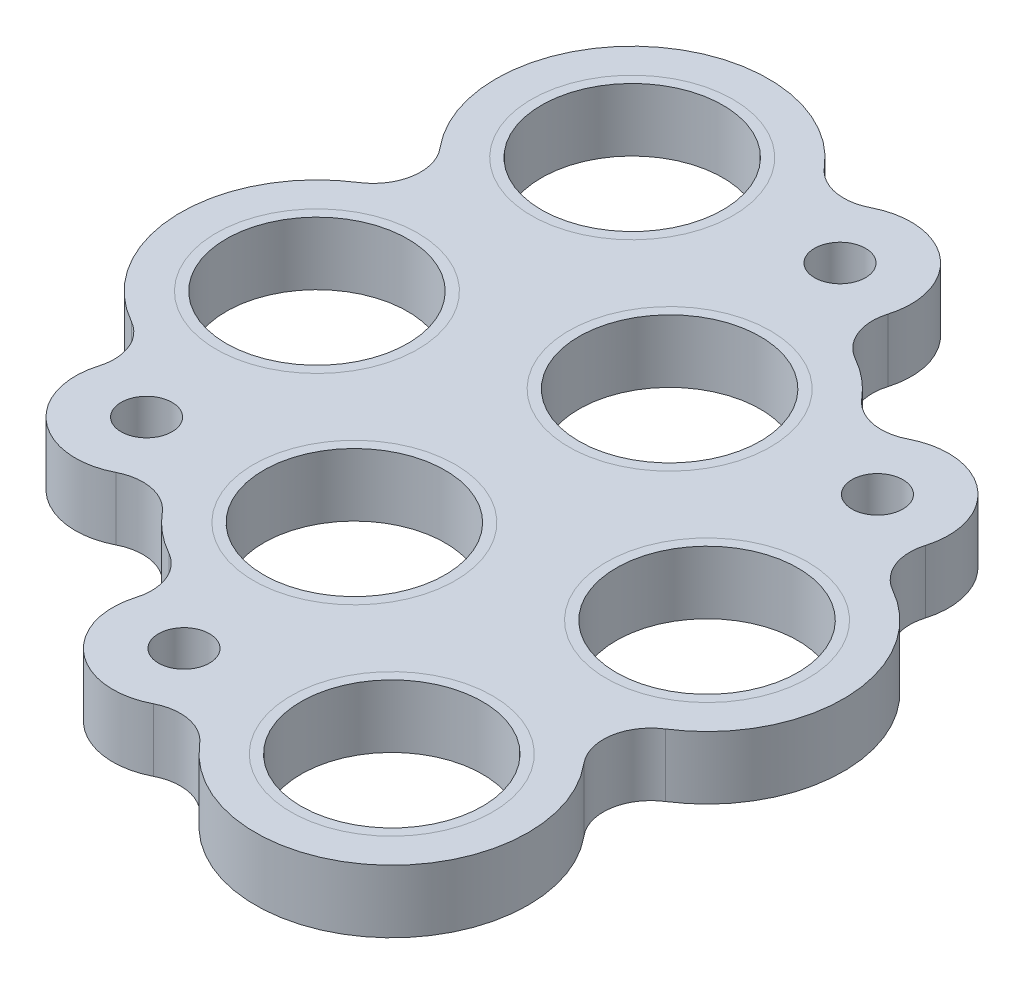
SolidWorks part; units mm, degrees
material "6061-T6 (SS)"
ref_plane "Front Plane" through (0, 0, 0) normal (0, 0, 1) x (1, 0, 0)
ref_plane "Top Plane" through (0, 0, 0) normal (0, 1, 0) x (1, 0, 0)
ref_plane "Right Plane" through (0, 0, 0) normal (1, 0, 0) x (0, 0, -1)
sketch "Sketch3" plane through (0, 0, 0) normal (0, 1, 0) x (1, 0, 0)
  line L0 (660.0708, -1265.9978) -> (682.0744, -1258.2621) construction
  circle A0 centre (645.1252, -1227.6229) radius 7.65
  circle A1 centre (663.5998, -1242.9425) radius 7.65
  circle A2 centre (682.0744, -1258.2621) radius 7.65
  circle A3 centre (678.5454, -1281.3174) radius 7.65
  circle A4 centre (660.0708, -1265.9978) radius 7.65
  circle A5 centre (641.5962, -1250.6782) radius 7.65
  arc A6 (653.9445, -1220.2424) -> (636.3279, -1235.0295) centre (645.1252, -1227.6229) ccw
  arc A12 (672.419, -1235.562) -> (669.2203, -1232.9095) centre (663.5998, -1242.9425) ccw
  arc A13 (667.3416, -1228.278) -> (658.8437, -1221.2313) centre (661.5913, -1226.5652) ccw
  arc A14 (635.4172, -1240.9792) -> (635.9757, -1260.7112) centre (641.5962, -1250.6782) ccw
  arc A15 (688.2534, -1267.9611) -> (687.6948, -1248.2291) centre (682.0744, -1258.2621) ccw
  arc A16 (651.2516, -1273.3782) -> (654.4503, -1276.0307) centre (660.0708, -1265.9978) ccw
  arc A17 (685.8162, -1243.5976) -> (677.3183, -1236.5509) centre (680.0659, -1241.8848) ccw
  arc A18 (637.8544, -1265.3427) -> (646.3523, -1272.3894) centre (643.6047, -1267.0555) ccw
  arc A19 (669.7261, -1288.6978) -> (687.3427, -1273.9108) centre (678.5454, -1281.3174) ccw
  arc A20 (656.329, -1280.6623) -> (664.8269, -1287.709) centre (662.0793, -1282.3751) ccw
  arc A21 (637.7465, -1265.759) -> (645.9632, -1272.5725) centre (643.6047, -1267.0555) ccw construction
  arc A22 (636.3279, -1235.0295) -> (635.4172, -1240.9792) centre (633.268, -1237.6057) cw
  arc A23 (637.8544, -1265.3427) -> (635.9757, -1260.7112) centre (634.0208, -1264.2009) ccw
  arc A24 (646.3523, -1272.3894) -> (651.2516, -1273.3782) centre (648.184, -1275.9454) cw
  arc A25 (656.329, -1280.6623) -> (654.4503, -1276.0307) centre (652.4954, -1279.5205) ccw
  arc A26 (664.8269, -1287.709) -> (669.7261, -1288.6978) centre (666.6586, -1291.265) cw
  arc A27 (687.3427, -1273.9108) -> (688.2534, -1267.9611) centre (690.4026, -1271.3346) cw
  arc A28 (685.8162, -1243.5976) -> (687.6948, -1248.2291) centre (689.6498, -1244.7394) ccw
  arc A29 (677.3183, -1236.5509) -> (672.419, -1235.562) centre (675.4866, -1232.9949) cw
  arc A30 (667.3416, -1228.278) -> (669.2203, -1232.9095) centre (671.1752, -1229.4198) ccw
  arc A31 (658.8437, -1221.2313) -> (653.9445, -1220.2424) centre (657.012, -1217.6753) cw
  arc A32 (653.5879, -1219.8362) -> (639.8237, -1217.4178) centre (645.1252, -1227.6229) ccw construction
  circle A33 centre (643.6047, -1267.0555) radius 2.15
  circle A34 centre (662.0793, -1282.3751) radius 2.15
  circle A35 centre (680.0659, -1241.8848) radius 2.15
  circle A36 centre (661.5913, -1226.5652) radius 2.15
  dimension "D1" = 4.3
  dimension "D2" = 15.3
  dimension "D3" = 4
extrude "Boss-Extrude1" add sketch "Sketch3" along normal blind 5.3
chamfer "Chamfer1" [suppressed] distance 0.3 angle 45
sketch "Sketch4" plane through (0, 5.3, 0) normal (0, 1, 0) x (1, 0, 0)
  circle A0 centre (682.0744, -1258.2621) radius 8.5
  circle A1 centre (678.5454, -1281.3174) radius 8.5
  circle A2 centre (660.0708, -1265.9978) radius 8.5
  circle A3 centre (663.5998, -1242.9425) radius 8.5
  circle A4 centre (641.5962, -1250.6782) radius 8.5
  circle A5 centre (645.1252, -1227.6229) radius 8.5
  dimension "D1" = 17
split line "Split Line2"
sketch "Sketch5" plane through (0, 0, 0) normal (0, -1, 0) x (1, 0, 0)
  circle A0 centre (643.6047, 1267.0555) radius 4
  circle A1 centre (662.0793, 1282.3751) radius 4
  circle A2 centre (680.0659, 1241.8848) radius 4
  circle A3 centre (661.5913, 1226.5652) radius 4
  dimension "D1" = 8
split line "Split Line3"
